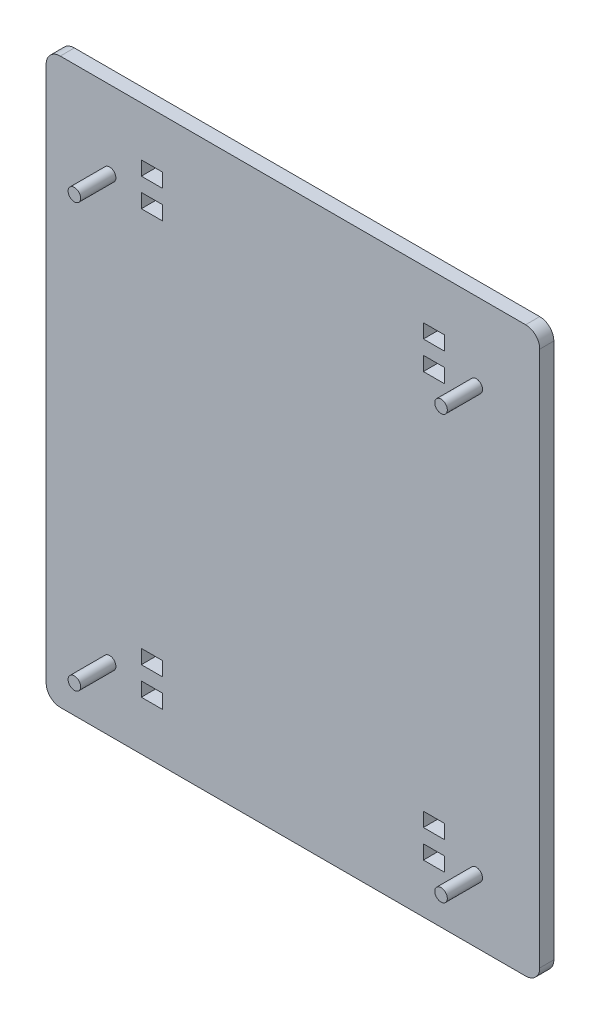
SolidWorks part; units mm, degrees
ref_plane "Front Plane" through (0, 0, 0) normal (0, 0, 1) x (1, 0, 0)
ref_plane "Top Plane" through (0, 0, 0) normal (0, 1, 0) x (1, 0, 0)
ref_plane "Right Plane" through (0, 0, 0) normal (1, 0, 0) x (0, 0, -1)
sketch "Sketch1" plane through (0, 0, 0) normal (0, 0, 1) x (1, 0, 0)
  line L1 (0, 101.6) -> (88.9, 101.6)
  line L2 (0, 101.6) -> (0, 0)
  line L3 (0, 0) -> (88.9, 0)
  line L4 (88.9, 101.6) -> (88.9, 0)
  dimension "D4" = 88.9
  dimension "D5" = 101.6
extrude "Boss-Extrude1" add sketch "Sketch1" along normal blind 2.54
sketch "Sketch2" plane through (0, 0, 2.54) normal (0, 0, 1) x (1, 0, 0)
  line L0 (11.43, 87.6046) -> (77.47, 87.6046) construction
  line L5 (77.47, 87.6046) -> (77.47, 11.4046) construction
  line L6 (77.47, 11.4046) -> (11.43, 11.4046) construction
  line L7 (11.43, 11.4046) -> (11.43, 87.6046) construction
  line L8 (44.45, 101.6) -> (44.45, 0) construction
  line L9 (11.43, 49.5046) -> (77.47, 49.5046) construction
  line L10 (0, 0) -> (88.9, 0) construction
  line L11 (88.9, 101.6) -> (0, 101.6) construction
  circle A0 centre (11.43, 87.6046) radius 1.1303
  circle A1 centre (77.47, 87.6046) radius 1.1303
  circle A2 centre (77.47, 11.4046) radius 1.1303
  circle A3 centre (11.43, 11.4046) radius 1.1303
  point P18 (44.45, 49.5046)
  point P22 (44.45, 50.8)
  dimension "D3" = 2.2606
  dimension "D1" = 76.2
  dimension "D2" = 66.04
  dimension "D4" = 1.2954
extrude "Boss-Extrude2" add sketch "Sketch2" along normal blind 6.35
sketch "Sketch3" plane through (0, 0, 2.54) normal (0, 0, 1) x (1, 0, 0)
  line L0 (0, 101.6) -> (0, 0) construction
  line L5 (88.9, 0) -> (88.9, 101.6) construction
  line L7 (44.45, 88.9) -> (44.45, 12.7) construction
  line L9 (0, 50.8) -> (88.9, 50.8) construction
  line L10 (19.05, 88.9) -> (69.85, 88.9) construction
  line L11 (19.05, 12.7) -> (69.85, 12.7) construction
  line L29 (19.05, 15.24) -> (19.05, 10.16) construction
  line L34 (20.955, 15.24) -> (17.145, 15.24) construction
  line L39 (20.955, 16.51) -> (17.145, 16.51)
  line L44 (20.955, 16.51) -> (20.955, 13.97)
  line L45 (69.85, 10.16) -> (69.85, 15.24) construction
  line L46 (67.945, 10.16) -> (71.755, 10.16) construction
  line L47 (67.945, 11.43) -> (71.755, 11.43)
  line L48 (67.945, 11.43) -> (67.945, 8.89)
  line L49 (67.945, 8.89) -> (71.755, 8.89)
  line L50 (71.755, 11.43) -> (71.755, 8.89)
  line L51 (67.945, 15.24) -> (71.755, 15.24) construction
  line L52 (67.945, 16.51) -> (71.755, 16.51)
  line L53 (67.945, 16.51) -> (67.945, 13.97)
  line L54 (67.945, 13.97) -> (71.755, 13.97)
  line L55 (71.755, 16.51) -> (71.755, 13.97)
  line L56 (20.955, 13.97) -> (17.145, 13.97)
  line L57 (17.145, 16.51) -> (17.145, 13.97)
  line L58 (17.145, 10.16) -> (20.955, 10.16) construction
  line L59 (17.145, 11.43) -> (20.955, 11.43)
  line L60 (17.145, 11.43) -> (17.145, 8.89)
  line L61 (17.145, 8.89) -> (20.955, 8.89)
  line L62 (20.955, 11.43) -> (20.955, 8.89)
  line L63 (19.05, 86.36) -> (19.05, 91.44) construction
  line L64 (17.145, 86.36) -> (20.955, 86.36) construction
  line L65 (17.145, 87.63) -> (20.955, 87.63)
  line L66 (17.145, 87.63) -> (17.145, 85.09)
  line L67 (17.145, 85.09) -> (20.955, 85.09)
  line L68 (20.955, 87.63) -> (20.955, 85.09)
  line L69 (17.145, 91.44) -> (20.955, 91.44) construction
  line L70 (17.145, 92.71) -> (20.955, 92.71)
  line L71 (17.145, 92.71) -> (17.145, 90.17)
  line L72 (17.145, 90.17) -> (20.955, 90.17)
  line L73 (20.955, 92.71) -> (20.955, 90.17)
  line L74 (69.85, 86.36) -> (69.85, 91.44) construction
  line L75 (67.945, 86.36) -> (71.755, 86.36) construction
  line L76 (67.945, 87.63) -> (71.755, 87.63)
  line L77 (67.945, 87.63) -> (67.945, 85.09)
  line L78 (67.945, 85.09) -> (71.755, 85.09)
  line L79 (71.755, 87.63) -> (71.755, 85.09)
  line L80 (67.945, 91.44) -> (71.755, 91.44) construction
  line L81 (67.945, 92.71) -> (71.755, 92.71)
  line L82 (67.945, 92.71) -> (67.945, 90.17)
  line L83 (67.945, 90.17) -> (71.755, 90.17)
  line L84 (71.755, 92.71) -> (71.755, 90.17)
  point P10 (44.45, 50.8)
  dimension "D3" = 50.8
  dimension "D1" = 5.08
  dimension "D2" = 3.81
  dimension "D4" = 76.2
  dimension "D5" = 2.54
extrude "Cut-Extrude1" cut sketch "Sketch3" against normal up to surface (2.54 mm away) up to face at (44.45, 50.8, 0)
fillet "Fillet1" radius 2.54 4 edges at (0, 0, 1.27) (88.9, 0, 1.27) (88.9, 101.6, 1.27) (0, 101.6, 1.27)
